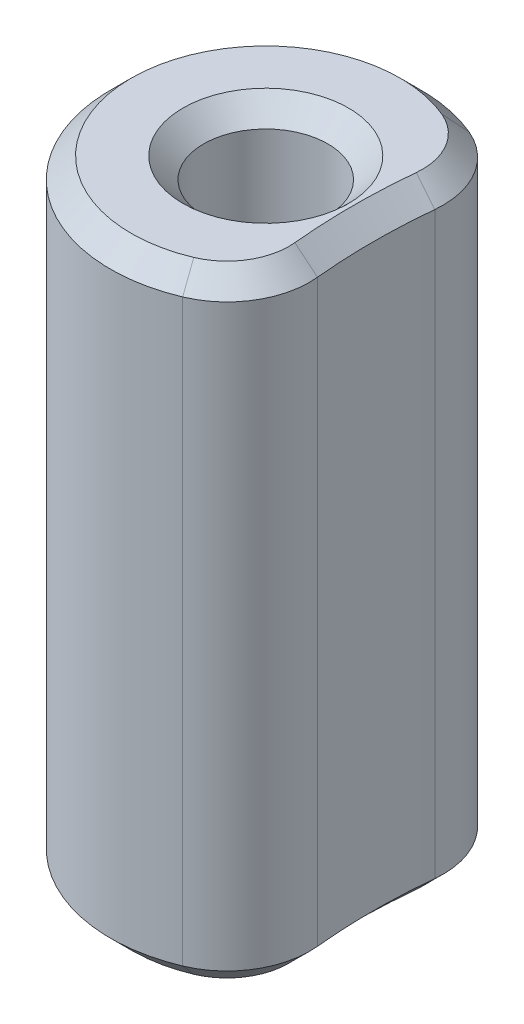
SolidWorks part; units mm, degrees
material "PLA/ABS"
ref_plane "Front Plane" through (0, 0, 0) normal (0, 0, 1) x (1, 0, 0)
ref_plane "Top Plane" through (0, 0, 0) normal (0, 1, 0) x (1, 0, 0)
ref_plane "Right Plane" through (0, 0, 0) normal (1, 0, 0) x (0, 0, -1)
sketch "Sketch1" plane through (0, 0, 0) normal (0, 1, 0) x (1, 0, 0)
  line L0 (0, 0) -> (21.5526, 0) construction
  line L1 (0, 0) -> (21.5526, 21.5526) construction
  line L2 (21.5526, 21.5526) -> (21.5526, 0) construction
  circle A0 centre (0, 0) radius 1.905
  circle A1 centre (21.5526, 0) radius 18 construction
  arc A2 (3.5724, -3.1495) -> (3.5724, 3.1495) centre (21.5526, 0) cw
  arc A3 (3.5724, 3.1495) -> (3.5724, -3.1495) centre (0, 0) ccw
  point P5 (2.5524, -4.0208)
  point P9 (2.9021, -2.2989)
  dimension "D1" = 3.81
  dimension "D2" = 36
  dimension "D4" = 4.7625
  dimension "D5" = 0.254
  dimension "D3" = 30.48
extrude "Boss-Extrude1" add sketch "Sketch1" along normal mid plane 19.05
fillet "Fillet1" radius 2.54 2 edges at (3.5724, 0, 3.1495) (3.5724, 0, -3.1495)
chamfer "Chamfer1" distance 0.635 angle 45 10 edges at (0, -9.525, 1.905) (3.0418, -9.525, 3.3497) (3.2986, -9.525, 0) (3.0418, -9.525, -3.3497) (-4.7625, -9.525, 0) (0, 9.525, 1.905) (3.0418, 9.525, 3.3497) (-4.7625, 9.525, 0) (3.0418, 9.525, -3.3497) (3.2986, 9.525, 0)
